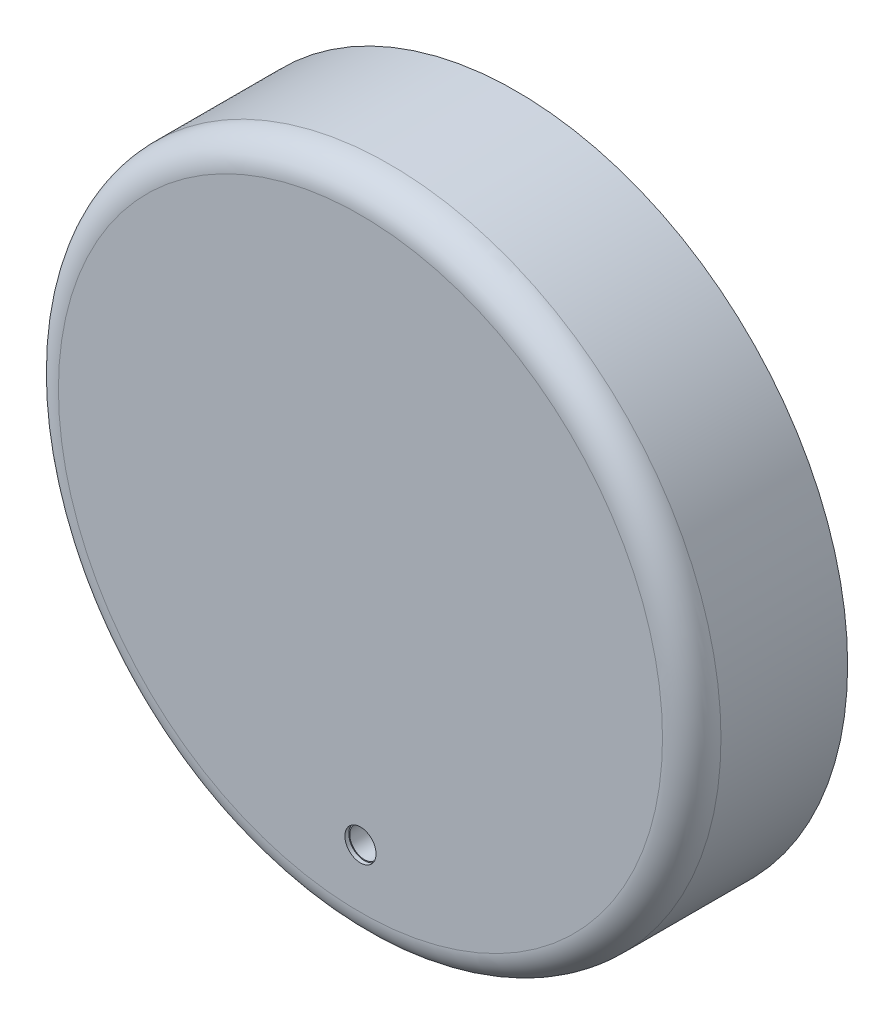
SolidWorks part; units mm, degrees
ref_plane "Front Plane" through (0, 0, 0) normal (0, 0, 1) x (1, 0, 0)
ref_plane "Top Plane" through (0, 0, 0) normal (0, 1, 0) x (1, 0, 0)
ref_plane "Right Plane" through (0, 0, 0) normal (1, 0, 0) x (0, 0, -1)
sketch "Sketch1" plane through (0, 0, 0) normal (0, 0, 1) x (1, 0, 0)
  circle A0 centre (0, 0) radius 31.5
  circle A1 centre (0, 0) radius 34
  dimension "D1" = 63
  dimension "D2" = 68
extrude "Boss-Extrude1" add sketch "Sketch1" along normal blind 13
sketch "Sketch2" plane through (0, 0, 13) normal (0, 0, 1) x (1, 0, 0)
  circle A0 centre (0, 0) radius 34
  dimension "D1" = 68
extrude "Boss-Extrude2" add sketch "Sketch2" along normal blind 3
fillet "Fillet1" radius 3 1 edges at (34, 0, 16)
sketch "Sketch3" plane through (0, 0, 13) normal (0, 0, -1) x (-1, 0, 0)
  circle A0 centre (-20, 0) radius 2.5
  circle A1 centre (20, 0) radius 2.5
  circle A2 centre (-20, 0) radius 1.5
  circle A3 centre (20, 0) radius 1.5
  dimension "D1" = 20
  dimension "D2" = 20
  dimension "D3" = 5
  dimension "D4" = 5
  dimension "D5" = 3
  dimension "D6" = 3
extrude "Boss-Extrude3" add sketch "Sketch3" along normal blind 10
sketch "Sketch5" plane through (0, 0, 0) normal (0, 0, -1) x (-1, 0, 0)
  circle A0 centre (0, 0) radius 32.5
  circle A2 centre (0, 0) radius 31.5
  dimension "D1" = 63
  dimension "D2" = 65
extrude "Cut-Extrude1" cut sketch "Sketch5" against normal blind 3
sketch "Sketch6" plane through (0, 0, 16) normal (0, 0, 1) x (1, 0, 0)
  circle A0 centre (0, -25) radius 1.6
  dimension "D1" = 3.2
  dimension "D2" = 25
extrude "Cut-Extrude2" cut sketch "Sketch6" against normal blind 0.4
sketch "Sketch7" plane through (0, 0, 15.6) normal (0, 0, 1) x (1, 0, 0)
  circle A0 centre (0, -25) radius 1.5
  dimension "D1" = 3
extrude "Cut-Extrude3" cut sketch "Sketch7" against normal through all
